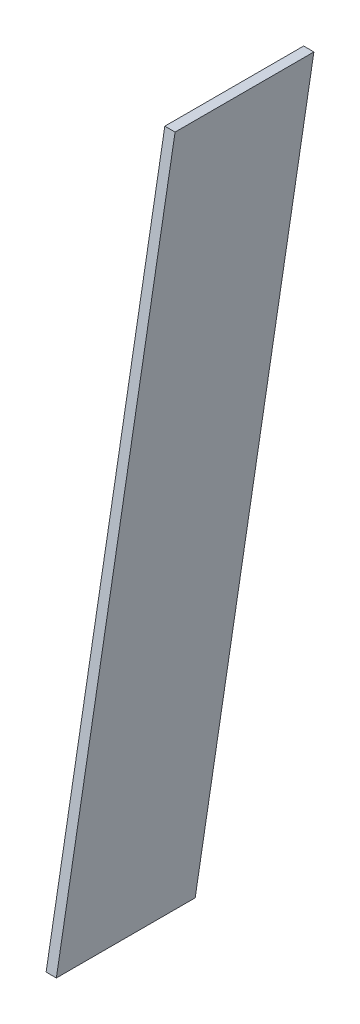
SolidWorks part; units mm, degrees
ref_plane "Front Plane" through (0, 0, 0) normal (0, 0, 1) x (1, 0, 0)
ref_plane "Top Plane" through (0, 0, 0) normal (0, 1, 0) x (1, 0, 0)
ref_plane "Right Plane" through (0, 0, 0) normal (1, 0, 0) x (0, 0, -1)
sketch "Sketch1" plane through (0, 0, 0) normal (1, 0, 0) x (0, 0, -1)
  line L0 (0, 0) -> (0, 456) construction
  line L1 (0, 0) -> (-1435.7806, 0) construction
  line L2 (0, 456) -> (-347.2964, -1513.6155)
  line L3 (-347.2964, -1513.6155) -> (-753.467, -1513.6155)
  line L4 (-753.467, -1513.6155) -> (-406.1706, 456)
  line L5 (-406.1706, 456) -> (0, 456)
  dimension "D1" = 400
  dimension "D2" = 10
  dimension "D3" = 1513.6155
  dimension "D4" = 456
  dimension "D5" = 2000
extrude "Boss-Extrude1" add sketch "Sketch1" along normal mid plane 30
